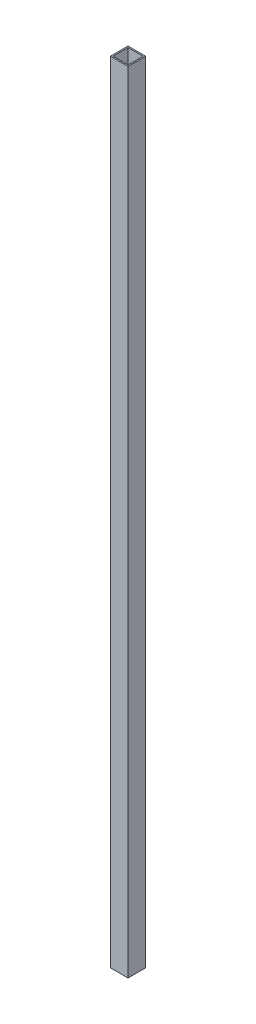
SolidWorks part; units mm, degrees
material "6063-T6"
ref_plane "Front Plane" through (0, 0, 0) normal (0, 0, 1) x (1, 0, 0)
ref_plane "Top Plane" through (0, 0, 0) normal (0, 1, 0) x (1, 0, 0)
ref_plane "Right Plane" through (0, 0, 0) normal (1, 0, 0) x (0, 0, -1)
sketch "Sketch1" plane through (0, 0, 0) normal (0, 1, 0) x (1, 0, 0)
  line L0 (3.175, 3.175) -> (3.175, 41.275)
  line L1 (0, 0) -> (44.45, 0)
  line L2 (0, 0) -> (0, 44.45)
  line L3 (0, 44.45) -> (44.45, 44.45)
  line L4 (44.45, 0) -> (44.45, 44.45)
  line L5 (3.175, 41.275) -> (41.275, 41.275)
  line L6 (41.275, 3.175) -> (41.275, 41.275)
  line L7 (3.175, 3.175) -> (41.275, 3.175)
  dimension "D1" = 44.45
  dimension "D2" = 3.175
extrude "Boss-Extrude1" add sketch "Sketch1" along normal blind 1985.9625
